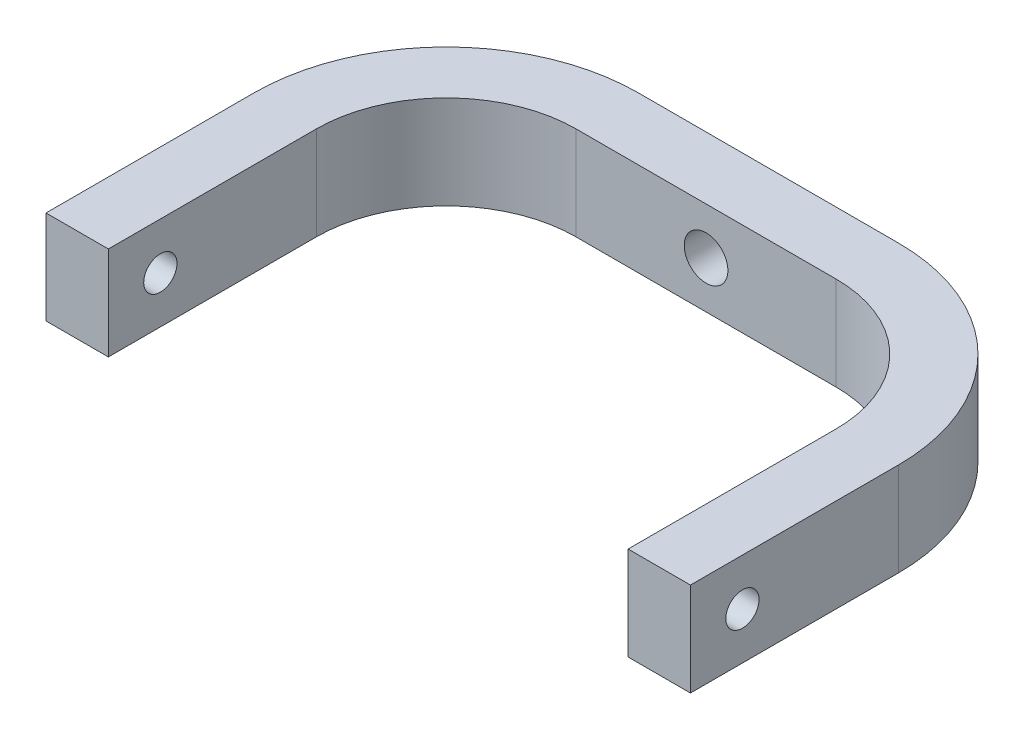
SolidWorks part; units mm, degrees
ref_plane "Front Plane" through (0, 0, 0) normal (0, 0, 1) x (1, 0, 0)
ref_plane "Top Plane" through (0, 0, 0) normal (0, 1, 0) x (1, 0, 0)
ref_plane "Right Plane" through (0, 0, 0) normal (1, 0, 0) x (0, 0, -1)
sketch "Sketch1" plane through (0, 0, 0) normal (0, 1, 0) x (1, 0, 0)
  line L0 (-70.0337, -37.9213) -> (-58.0337, -37.9213)
  line L1 (-58.0337, -37.9213) -> (-58.0337, 2.0787)
  line L2 (-70.0337, 2.0787) -> (-70.0337, -37.9213)
  line L3 (-8.0337, 27.0787) -> (-33.0337, 27.0787)
  line L4 (-33.0337, 39.0787) -> (-8.0337, 39.0787)
  line L5 (-8.0337, 39.0787) -> (-8.0337, 27.0787)
  arc A0 (-58.0337, 2.0787) -> (-33.0337, 27.0787) centre (-33.0337, 2.0787) cw
  arc A1 (-70.0337, 2.0787) -> (-33.0337, 39.0787) centre (-33.0337, 2.0787) cw
  point P9 (0, 0)
  point P11 (0, 0)
  point P12 (0, 0)
  point P13 (0.5056, 60.8427)
  point P14 (-3.7079, 44.6629)
  point P15 (10.2809, 54.2697)
  point P16 (-5.0562, 47.0225)
  point P17 (0, 0)
  point P18 (0, 0)
  point P19 (-9.9438, 45.3371)
  point P20 (-9.7753, 42.3034)
  point P21 (-46.5169, -38.0899)
  point P22 (-51.9101, -37.9213)
  point P23 (0, 0)
  dimension "D1" = 12
  dimension "D2" = 40
  dimension "D3" = 25
  dimension "D4" = 25
extrude "Boss-Extrude1" add sketch "Sketch1" along normal blind 18
mirror "Mirror1" about plane through (-8.0337, 18, -39.0787) normal (-1, 0, 0) of "Boss-Extrude1"
sketch "Sketch2" plane through (-58.0337, 0, 0) normal (1, 0, 0) x (0, 0, -1)
  line L0 (-27.9213, 18) -> (-27.9213, 0) construction
  line L1 (-37.9213, 18) -> (2.0787, 18) construction
  line L2 (-37.9213, 0) -> (2.0787, 0) construction
  line L3 (-37.9213, 18) -> (-37.9213, 0) construction
  circle A1 centre (-27.9213, 9) radius 3.2
  dimension "D1" = 6.4
  dimension "D2" = 10
extrude "Cut-Extrude1" cut sketch "Sketch2" against normal blind 40 and the other way blind 150 contours A1
sketch "Sketch3" plane through (0, 0, -27.0787) normal (0, 0, 1) x (1, 0, 0)
  line L0 (-33.0337, 18) -> (16.9663, 0) construction
  line L1 (-33.0337, 18) -> (-58.0337, 18) construction
  line L2 (-33.0337, 18) -> (-33.0337, 0) construction
  circle A0 centre (-8.0337, 9) radius 4.2
  dimension "D1" = 8.4
extrude "Cut-Extrude2" cut sketch "Sketch3" against normal blind 40
